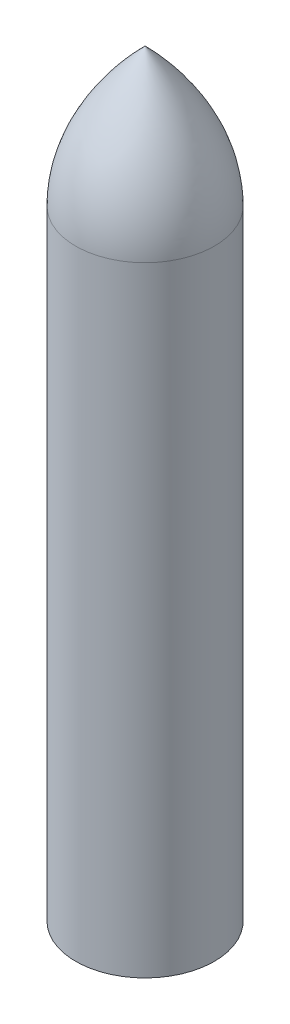
SolidWorks part; units mm, degrees
ref_plane "Front Plane" through (0, 0, 0) normal (0, 0, 1) x (1, 0, 0)
ref_plane "Top Plane" through (0, 0, 0) normal (0, 1, 0) x (1, 0, 0)
ref_plane "Right Plane" through (0, 0, 0) normal (1, 0, 0) x (0, 0, -1)
sketch "Sketch1" plane through (0, 0, 0) normal (0, 0, 1) x (1, 0, 0)
  line L0 (0, 0) -> (-150, 0)
  line L1 (-150, 0) -> (-150, 1340)
  line L2 (0, 0) -> (0, 1640)
  line L3 (0, 1640) -> (-150, 1490) construction
  line L4 (-150, 1490) -> (-150, 1340) construction
  line L5 (-150, 1340) -> (0, 1340) construction
  line L6 (-75, 1340) -> (-75, 1640) construction
  spline S0 degree 2 poles (0, 1640) (-150, 1490) (-150, 1340) knots 0 0 0 1 1 1
  point P9 (-75, 1640)
  point P10 (-75, 1490)
  dimension "D1" = 150
  dimension "D2" = 1640
  dimension "D3" = 300
revolve "Revolve1" add sketch "Sketch1" angle 360 about L2
